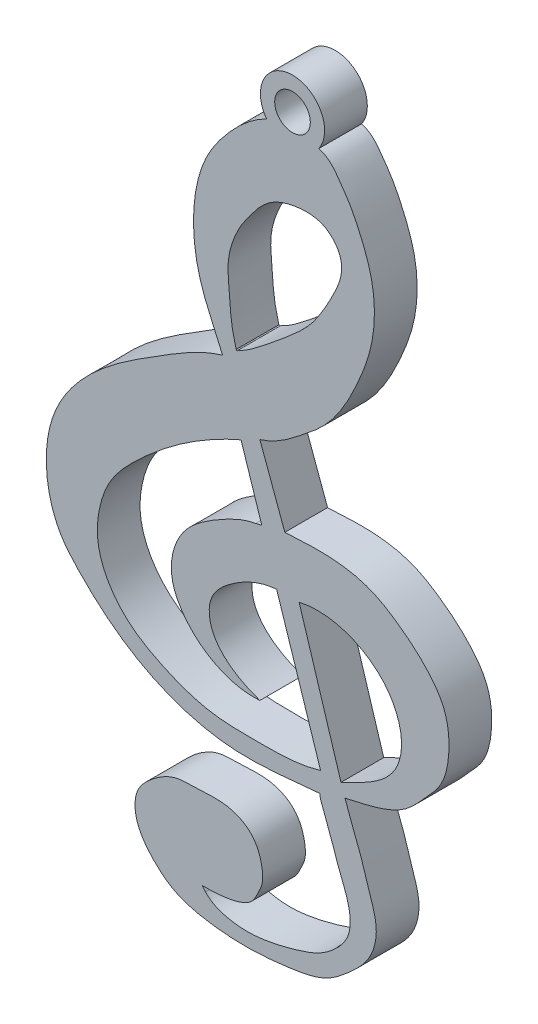
SolidWorks part; units mm, degrees
ref_plane "Alzado" through (0, 0, 0) normal (0, 0, 1) x (1, 0, 0)
ref_plane "Planta" through (0, 0, 0) normal (0, 1, 0) x (1, 0, 0)
ref_plane "Vista lateral" through (0, 0, 0) normal (1, 0, 0) x (0, 0, -1)
sketch "Croquis1" plane through (0, 0, 0) normal (0, 0, 1) x (1, 0, 0)
  line L0 (-75.7484, -1.1336) -> (-73.2794, -8.717)
  line L5 (-74.4845, -1.1336) -> (-72.133, -8.717)
  line L7 (-76.6889, 5.6788) -> (-75.2887, 1.8672)
  line L8 (-77.7478, 5.1343) -> (-76.5838, 1.5591)
  arc A0 (-76.3154, 21.4647) -> (-73.3828, 21.4852) centre (-74.8565, 22.5242) cw
  circle A1 centre (-74.8565, 22.5242) radius 1
  spline S0 degree 3 poles (-76.6889, -7.0122) (-77.7403, -6.6698) (-79.4933, -5.6873) (-79.6097, -3.2535) (-78.048, -1.8232) (-76.6909, -1.2167) (-75.7484, -1.1336) knots 0 0 0 0 0.383378 0.517271 0.709393 1 1 1 1
  spline S1 degree 3 poles (-74.4845, -1.1336) (-73.2834, -0.8503) (-71.4401, -1.186) (-69.6335, -2.6102) (-68.8354, -3.973) (-68.6446, -5.3768) (-69.0978, -6.878) (-70.4438, -7.9553) (-71.5945, -8.4367) (-72.133, -8.717) knots 0 0 0 0 0.278394 0.399127 0.515243 0.629976 0.711946 0.862107 1 1 1 1
  spline S2 degree 1 poles (-76.5838, 1.5591) (-76.9241, 1.4824) knots 0 0 1 1
  spline S3 degree 3 poles (-71.9061, -9.3746) (-71.6128, -10.2668) (-71.0368, -11.5531) (-70.5283, -13.3595) (-70.0007, -14.7942) (-70.3895, -16.5351) (-71.6151, -17.6996) (-73.0608, -18.8844) (-74.9552, -19.1998) (-77.2419, -19.4389) (-79.4431, -19.3178) (-81.4338, -18.831) (-82.4647, -17.9803) (-83.141, -17.2525) (-83.594, -16.4808) (-83.753, -15.6175) (-83.6086, -14.786) (-83.1948, -14.2635) (-82.7029, -13.8236) (-82.1793, -13.4417) (-81.4321, -13.0929) (-80.5171, -13.0643) (-79.4925, -13.0164) (-78.2791, -13.0205) (-77.0162, -13.6664) (-76.5552, -14.8621) (-76.4886, -15.8389) (-76.8153, -16.4589) (-77.0651, -17.0202) (-77.7429, -17.4017) (-78.7067, -17.6036) (-79.4827, -17.645) (-79.9251, -17.6291) knots 0 0 0 0 0.074805 0.111322 0.14963 0.194578 0.242981 0.281555 0.341328 0.390462 0.465399 0.516027 0.549473 0.569858 0.595053 0.619443 0.638198 0.660324 0.670723 0.690791 0.711746 0.735034 0.762614 0.79371 0.830998 0.866508 0.890979 0.905817 0.921676 0.93857 0.964779 1 1 1 1
  spline S4 degree 3 poles (-73.3261, -9.8533) (-74.9797, -9.9958) (-78.4523, -10.4954) (-83.3882, -8.9145) (-86.2754, -6.4951) (-87.9572, -4.5644) (-88.5703, -2.9966) (-88.7758, -1.0138) (-88.306, 1.7296) (-85.9495, 4.6766) (-82.4258, 6.8697) (-80.045, 8.3597) (-78.784, 8.7351) knots 0 0 0 0 0.144811 0.299823 0.432277 0.467633 0.520862 0.574899 0.639454 0.757272 0.887089 1 1 1 1
  spline S5 degree 3 poles (-76.6889, -7.0122) (-77.78, -7.1011) (-79.3542, -6.6115) (-80.9083, -5.1916) (-81.725, -3.7942) (-81.6647, -2.1508) (-80.9788, -0.8071) (-80.0413, -0.0147) (-79.2351, 0.5035) (-78.2614, 1.0513) (-77.5003, 1.381) (-76.9241, 1.4824) knots 0 0 0 0 0.229659 0.335098 0.446803 0.564327 0.67037 0.760787 0.823624 0.875763 1 1 1 1
  spline S6 degree 1 poles (-79.7458, -17.8518) (-79.9251, -17.6291) knots 0 0 1 1
  spline S8 degree 2 poles (-77.928, 9.3959) (-77.977, 9.3166) (-78.0222, 9.3959) knots 0 0 0 1 1 1
  spline S9 degree 1 poles (-78.8313, 8.8264) (-78.784, 8.7351) knots 0 0 1 1
  spline S10 degree 3 poles (-79.7458, -17.8518) (-79.3777, -18.2505) (-78.5989, -18.5102) (-77.4455, -18.6415) (-76.3348, -18.5475) (-75.1932, -18.2915) (-74.1574, -17.9828) (-73.3286, -17.6559) (-72.6748, -17.1966) (-72.1369, -16.6847) (-71.7251, -16.0782) (-71.5579, -15.2507) (-71.7293, -14.277) (-72.076, -13.4116) (-72.3775, -12.6602) (-72.5466, -12.0926) (-72.7482, -11.5883) (-72.8958, -11.1126) (-73.0653, -10.7008) (-73.2352, -10.2833) (-73.3173, -10.0266) (-73.3261, -9.8533) knots 0 0 0 0 0.100297 0.155435 0.22444 0.315021 0.381826 0.433978 0.486801 0.535484 0.577524 0.62671 0.694738 0.765896 0.807411 0.851577 0.880545 0.912597 0.948032 0.966789 1 1 1 1
  spline S11 degree 3 poles (-75.2887, 1.8672) (-74.4684, 1.9083) (-72.8726, 2.0155) (-70.6315, 1.6751) (-68.8104, 0.5656) (-67.3898, -0.6255) (-66.1537, -2.2567) (-65.9617, -4.235) (-66.3654, -6.0094) (-67.4592, -7.1482) (-68.2705, -8.1232) (-69.8547, -8.9598) (-71.0542, -9.1663) (-71.9061, -9.3746) knots 0 0 0 0 0.117623 0.23029 0.317393 0.419587 0.496457 0.603597 0.693697 0.746524 0.827441 0.873617 1 1 1 1
  spline S12 degree 3 poles (-78.0222, 9.3959) (-78.1122, 9.7431) (-78.2846, 10.4078) (-78.3642, 11.4094) (-78.4343, 12.3402) (-78.5129, 13.223) (-78.4001, 13.9972) (-78.1459, 14.7747) (-77.7823, 15.5588) (-77.2393, 16.3136) (-76.6981, 17.0181) (-75.9484, 17.6798) (-74.9224, 18.0194) (-73.9231, 18.1085) (-72.8265, 17.872) (-72.0628, 16.966) (-72.1028, 15.784) (-72.5205, 14.8564) (-73.1079, 13.753) (-73.7785, 12.7066) (-74.6781, 11.8512) (-75.6185, 11.0489) (-76.6284, 10.2348) (-77.4242, 9.6403) (-77.8677, 9.4252) (-77.928, 9.3959) knots 0 0 0 0 0.046234 0.0885 0.129376 0.166981 0.202561 0.229436 0.272508 0.313509 0.349202 0.387286 0.440603 0.485479 0.515571 0.583511 0.614582 0.664466 0.712997 0.776704 0.823501 0.872685 0.936377 0.99134 1 1 1 1
  spline S13 degree 3 poles (-73.2794, -8.717) (-74.544, -9.0993) (-76.5979, -9.0858) (-79.6446, -9.0681) (-81.9323, -8.2263) (-83.9574, -7.1106) (-85.2735, -5.6214) (-85.9149, -3.853) (-85.7599, -2.2014) (-85.2826, -0.736) (-84.3926, 0.4562) (-83.2708, 1.5397) (-81.2075, 3.3144) (-79.2824, 4.4725) (-77.7478, 5.1343) knots 0 0 0 0 0.140602 0.223478 0.328348 0.401005 0.472812 0.539193 0.598886 0.649529 0.704842 0.75815 0.818924 1 1 1 1
  spline S15 degree 3 poles (-78.784, 8.7351) (-79.1488, 9.6345) (-80.225, 11.6466) (-80.6129, 14.9502) (-79.9079, 17.8263) (-78.3797, 19.9213) (-77.2015, 21.0205) (-76.3154, 21.4647) knots 0 0 0 0 0.201336 0.468683 0.6683 0.798365 1 1 1 1
  spline S16 degree 3 poles (-73.3828, 21.4852) (-72.8163, 21.3526) (-72.29, 20.6179) (-71.5634, 19.5726) (-70.9554, 18.3033) (-70.1803, 16.2797) (-70.2101, 13.6244) (-71.1184, 11.2741) (-72.0347, 9.4313) (-73.061, 8.0932) (-74.1765, 7.2115) (-75.2453, 6.3414) (-76.1053, 5.8549) (-76.6889, 5.6788) knots 0 0 0 0 0.08272 0.135601 0.197596 0.299487 0.468924 0.591754 0.687029 0.786865 0.848882 0.906336 1 1 1 1
extrude "Saliente-Extruir1" add sketch "Croquis1" along normal blind 2.4 contours S16 A0 S15 S4 S10 S6 S3 S11 L7 A1 L5 S1 S8 S12 L0 S13 L8 S2 S5 S0
